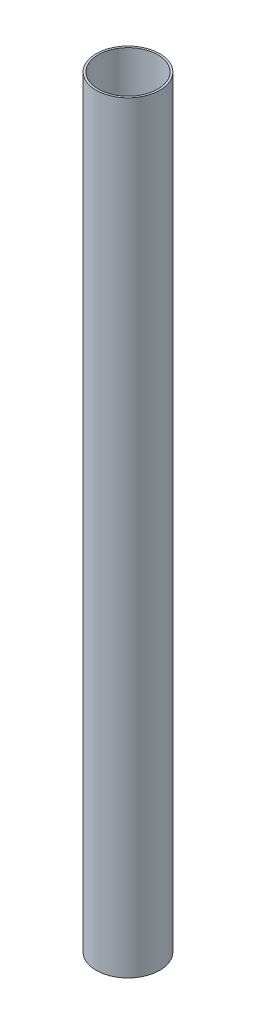
SolidWorks part; units mm, degrees
ref_plane "Front Plane" through (0, 0, 0) normal (0, 0, 1) x (1, 0, 0)
ref_plane "Top Plane" through (0, 0, 0) normal (0, 1, 0) x (1, 0, 0)
ref_plane "Right Plane" through (0, 0, 0) normal (1, 0, 0) x (0, 0, -1)
sketch "Sketch1" plane through (0, 0, 0) normal (0, 1, 0) x (1, 0, 0)
  circle A0 centre (0, 0) radius 47.625
  circle A1 centre (0, 0) radius 50.8
  dimension "D1" = 101.6
  dimension "D2" = 3.175
extrude "Boss-Extrude1" add sketch "Sketch1" along normal blind 1219.2
